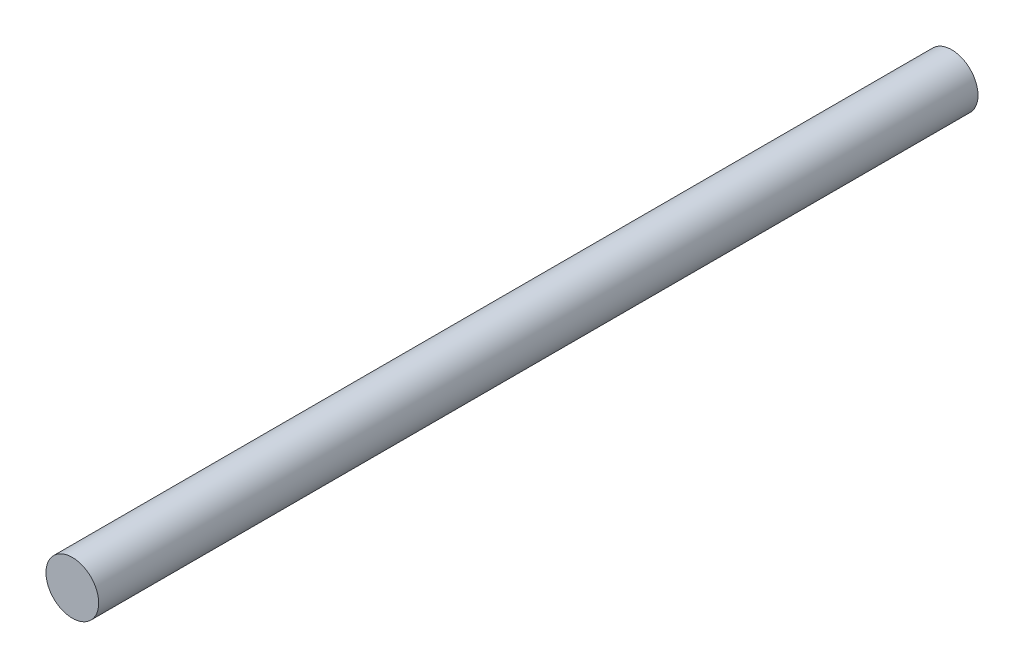
SolidWorks part; units mm, degrees
ref_plane "Plan de face" through (0, 0, 0) normal (0, 0, 1) x (1, 0, 0)
ref_plane "Plan de dessus" through (0, 0, 0) normal (0, 1, 0) x (1, 0, 0)
ref_plane "Plan de droite" through (0, 0, 0) normal (1, 0, 0) x (0, 0, -1)
sketch "Esquisse1" plane through (0, 0, 0) normal (0, 0, 1) x (1, 0, 0)
  circle A0 centre (0, 0) radius 30
extrude "Boss.-Extru.2" add sketch "Esquisse1" along normal blind 1000
